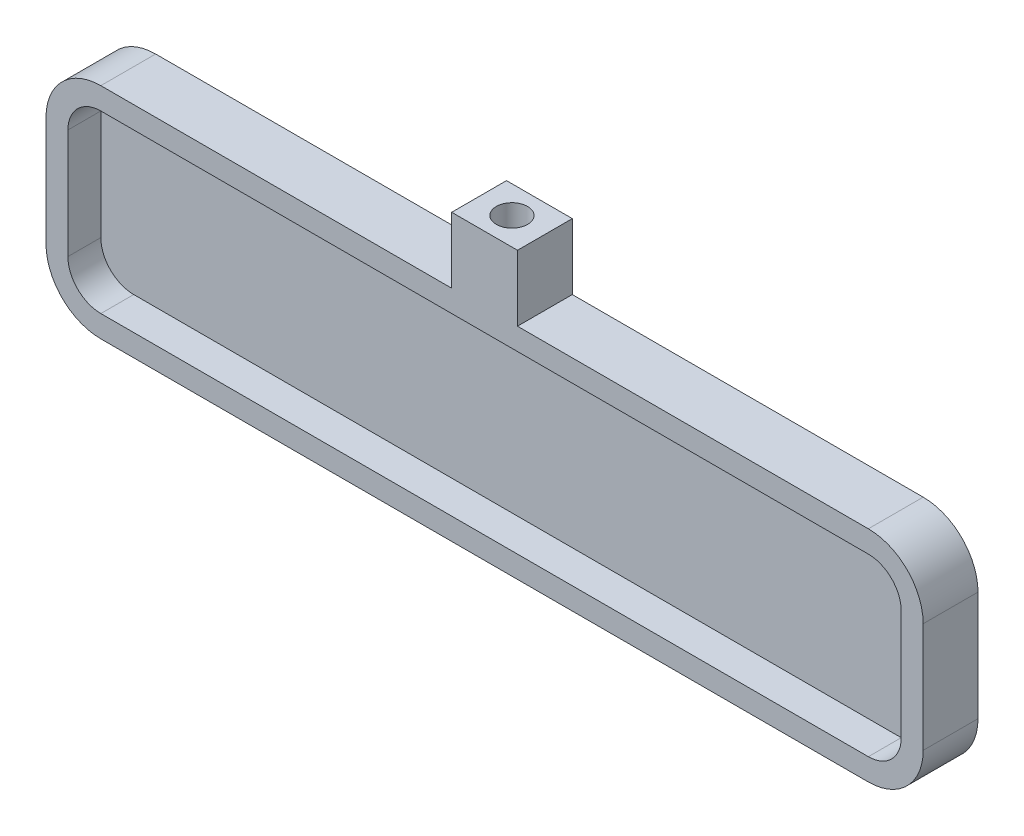
SolidWorks part; units mm, degrees
ref_plane "Front Plane" through (0, 0, 0) normal (0, 0, 1) x (1, 0, 0)
ref_plane "Top Plane" through (0, 0, 0) normal (0, 1, 0) x (1, 0, 0)
ref_plane "Right Plane" through (0, 0, 0) normal (1, 0, 0) x (0, 0, -1)
sketch "Sketch1" plane through (0, 0, 0) normal (0, 0, 1) x (1, 0, 0)
  line L1 (-40, 10) -> (40, 10)
  line L2 (-40, 10) -> (-40, -10)
  line L3 (-40, -10) -> (40, -10)
  line L4 (40, 10) -> (40, -10)
  line L5 (-40, 10) -> (40, -10) construction
  line L6 (-40, -10) -> (40, 10) construction
  point P0 (0, 0)
  dimension "D1" = 20
  dimension "D2" = 80
extrude "Boss-Extrude1" add sketch "Sketch1" along normal blind 5
fillet "Fillet1" radius 5 4 edges at (40, 10, 2.5) (40, -10, 2.5) (-40, -10, 2.5) (-40, 10, 2.5)
shell "Shell1" thickness 2
sketch "Sketch2" plane through (0, 10, 0) normal (0, 1, 0) x (1, 0, 0)
  line L0 (35, 0) -> (-35, 0) construction
  line L1 (3, -5) -> (-3, -5)
  line L2 (3, -5) -> (3, 0)
  line L3 (3, 0) -> (-3, 0)
  line L4 (-3, -5) -> (-3, 0)
  line L5 (3, -5) -> (-3, 0) construction
  line L6 (3, 0) -> (-3, -5) construction
  point P0 (0, -2.5)
  dimension "D1" = 5
  dimension "D2" = 6
extrude "Boss-Extrude2" add sketch "Sketch2" along normal blind 6
sketch "Sketch3" plane through (0, 16, 0) normal (0, 1, 0) x (1, 0, 0)
  line L0 (3, -2.5) -> (-3, -2.5) construction
  line L1 (3, -5) -> (3, 0) construction
  line L2 (-3, 0) -> (-3, -5) construction
  line L3 (0, 0) -> (0, -5) construction
  line L4 (3, 0) -> (-3, 0) construction
  line L5 (-3, -5) -> (3, -5) construction
  circle A0 centre (-0.0019, -2.5027) radius 1.425
  dimension "D1" = 2.85
extrude "Cut-Extrude1" cut sketch "Sketch3" against normal blind 4
